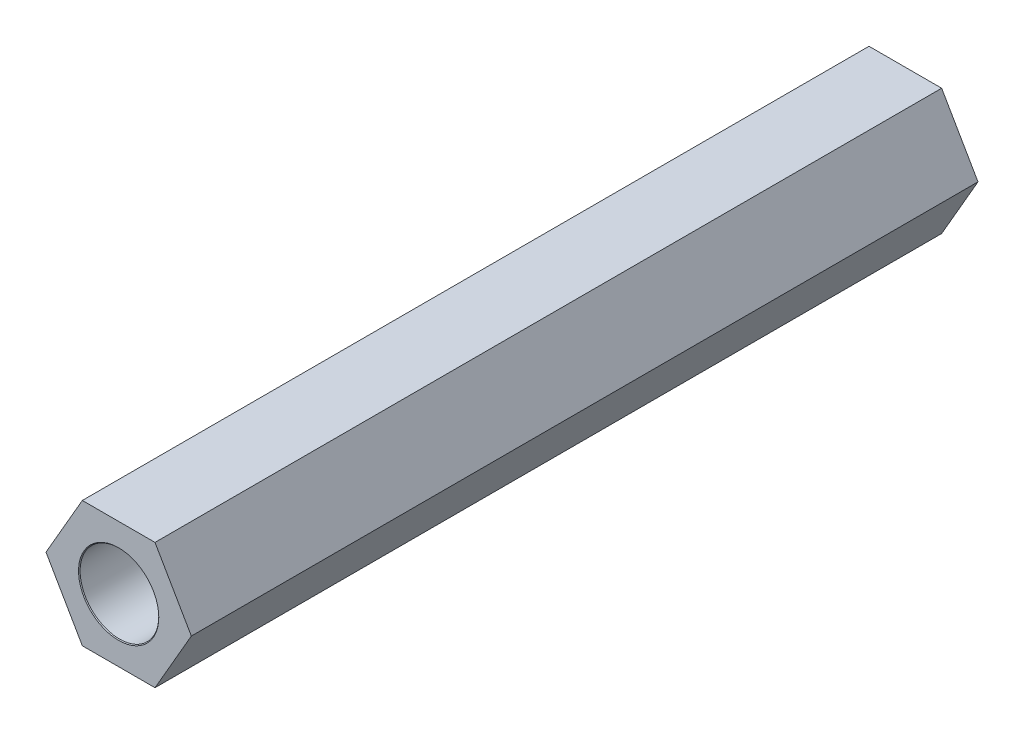
SolidWorks part; units mm, degrees
ref_plane "Front Plane" through (0, 0, 0) normal (0, 0, 1) x (1, 0, 0)
ref_plane "Top Plane" through (0, 0, 0) normal (0, 1, 0) x (1, 0, 0)
ref_plane "Right Plane" through (0, 0, 0) normal (1, 0, 0) x (0, 0, -1)
sketch "Sketch1" plane through (0, 0, 0) normal (0, 0, 1) x (1, 0, 0)
  line L1 (-83.6906, -116.6542) -> (-84.8453, -114.6542)
  line L2 (-84.8453, -114.6542) -> (-87.1547, -114.6542)
  line L3 (-87.1547, -114.6542) -> (-88.3094, -116.6542)
  line L4 (-88.3094, -116.6542) -> (-87.1547, -118.6542)
  line L5 (-87.1547, -118.6542) -> (-84.8453, -118.6542)
  line L6 (-84.8453, -118.6542) -> (-83.6906, -116.6542)
  circle A0 centre (-86, -116.6542) radius 2 construction
  dimension "D1" = 4
extrude "Boss-Extrude1" add sketch "Sketch1" along normal up to surface (25 mm away)
hole_wizard "Ø2.5mm Dowel Hole2" positions "3DSketch2" profile "Sketch3" hole size "Ø2.5" standard "ISO" end condition through all
sketch3d "3DSketch2"
  circle A0 centre (-86, -116.6542, -0.025) radius 1 construction
  point P0 (-86, -116.6542, 25)
  point P5 (-86, -116.6542, 0.975)
sketch "Sketch3" plane through (-86, -116.6542, 25) normal (1, 0, 0) x (0, -1, 0)
  line L0 (0, 0) -> (0, 25)
  line L1 (0, 25) -> (1.25, 25)
  line L2 (1.25, 25) -> (1.25, 0.025)
  line L3 (1.25, 0.025) -> (1.275, 0)
  line L5 (1.275, 0) -> (0, 0)
  line L6 (-1.25, 0.025) -> (-1.275, 0) construction
  line L11 (0, -6.35) -> (0, 107.95) construction
  dimension "Thru Hole Dia." = 2.5
  dimension "Thru Hole Depth" = 25
  dimension "Near C'Sink Dia." = 2.55
  dimension "Near C'Sink Angle" = 90
